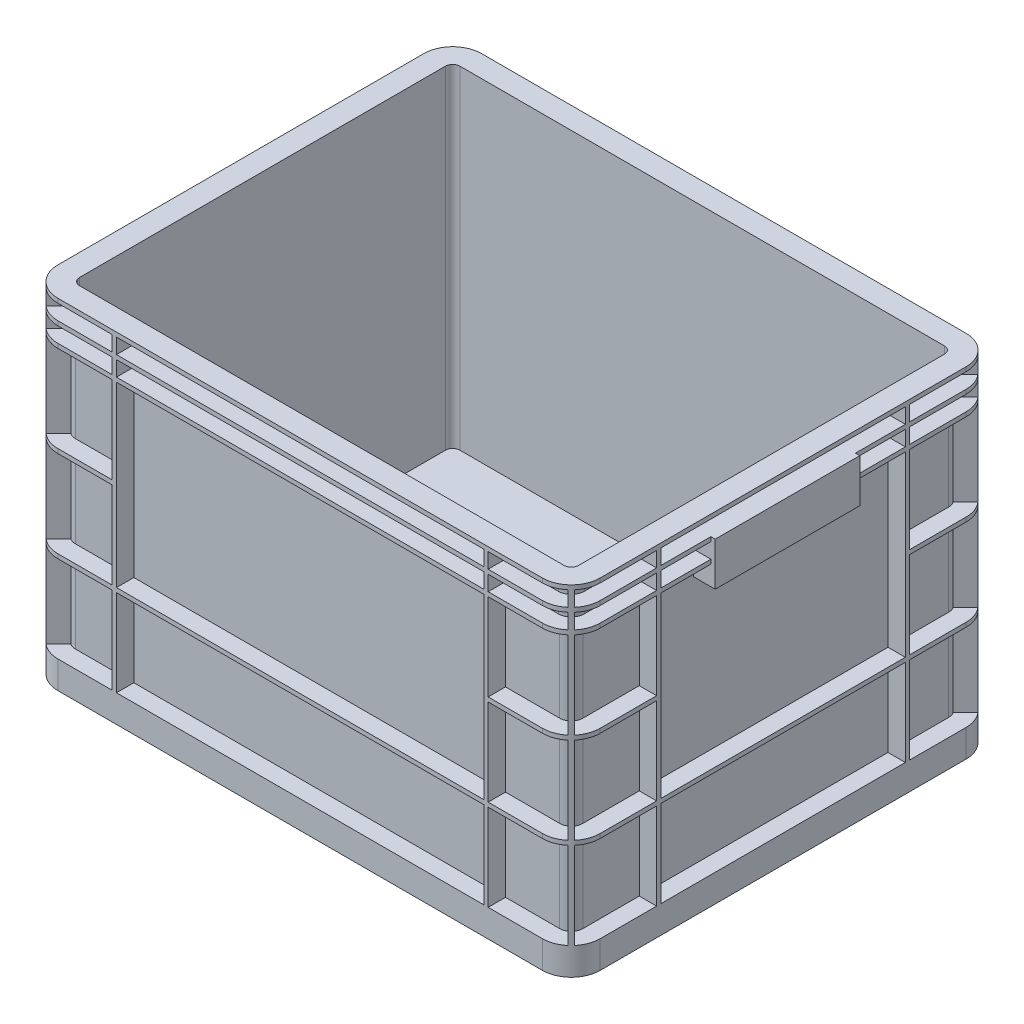
SolidWorks part; units mm, degrees
ref_plane "Front Plane" through (0, 0, 0) normal (0, 0, 1) x (1, 0, 0)
ref_plane "Top Plane" through (0, 0, 0) normal (0, 1, 0) x (1, 0, 0)
ref_plane "Right Plane" through (0, 0, 0) normal (1, 0, 0) x (0, 0, -1)
sketch "Sketch1" plane through (0, 0, 0) normal (0, 1, 0) x (1, 0, 0)
  line L1 (0, 0) -> (375, 0)
  line L2 (0, 0) -> (0, 293)
  line L3 (0, 293) -> (375, 293)
  line L4 (375, 0) -> (375, 293)
  dimension "D1" = 375
  dimension "D2" = 293
extrude "Boss-Extrude1" add sketch "Sketch1" along normal blind 240
fillet "Fillet1" radius 20 4 edges at (0, 120, -293) (375, 120, -293) (0, 120, 0) (375, 120, 0)
sketch "Sketch2" plane through (0, 240, 0) normal (0, 1, 0) x (1, 0, 0)
  line L8 (355, 278) -> (20, 278)
  line L9 (15, 273) -> (15, 20)
  line L10 (20, 15) -> (355, 15)
  line L11 (360, 20) -> (360, 273)
  line L12 (355, 278) -> (20, 278)
  line L13 (15, 273) -> (15, 20)
  line L14 (20, 15) -> (355, 15)
  line L15 (360, 20) -> (360, 273)
  arc A8 (20, 278) -> (15, 273) centre (20, 273) ccw
  arc A9 (15, 20) -> (20, 15) centre (20, 20) ccw
  arc A10 (355, 15) -> (360, 20) centre (355, 20) ccw
  arc A11 (360, 273) -> (355, 278) centre (355, 273) ccw
  arc A12 (20, 278) -> (15, 273) centre (20, 273) ccw
  arc A13 (15, 20) -> (20, 15) centre (20, 20) ccw
  arc A14 (355, 15) -> (360, 20) centre (355, 20) ccw
  arc A15 (360, 273) -> (355, 278) centre (355, 273) ccw
  dimension "D1" = 15
extrude "Cut-Extrude1" cut sketch "Sketch2" against normal blind 230
sketch "Sketch3" plane through (0, 0, 0) normal (0, -1, 0) x (1, 0, 0)
  line L0 (365, -273) -> (365, -20)
  line L1 (355, -10) -> (20, -10)
  line L2 (10, -20) -> (10, -273)
  line L3 (20, -283) -> (355, -283)
  line L4 (0, -20) -> (0, -273)
  line L5 (20, -293) -> (355, -293)
  line L6 (375, -273) -> (375, -20)
  line L7 (355, 0) -> (20, 0)
  line L8 (0, -20) -> (0, -273)
  line L9 (20, -293) -> (355, -293)
  line L10 (375, -273) -> (375, -20)
  line L11 (355, 0) -> (20, 0)
  arc A0 (365, -20) -> (355, -10) centre (355, -20) ccw
  arc A1 (20, -10) -> (10, -20) centre (20, -20) ccw
  arc A2 (10, -273) -> (20, -283) centre (20, -273) ccw
  arc A3 (355, -283) -> (365, -273) centre (355, -273) ccw
  arc A4 (0, -273) -> (20, -293) centre (20, -273) ccw
  arc A5 (355, -293) -> (375, -273) centre (355, -273) ccw
  arc A6 (375, -20) -> (355, 0) centre (355, -20) ccw
  arc A7 (20, 0) -> (0, -20) centre (20, -20) ccw
  arc A8 (0, -273) -> (20, -293) centre (20, -273) ccw
  arc A9 (355, -293) -> (375, -273) centre (355, -273) ccw
  arc A10 (375, -20) -> (355, 0) centre (355, -20) ccw
  arc A11 (20, 0) -> (0, -20) centre (20, -20) ccw
  dimension "D1" = 0
  dimension "D2" = 10
extrude "Cut-Extrude2" cut sketch "Sketch3" against normal blind 5
sketch "Sketch4" plane through (0, 0, 0) normal (0, -1, 0) x (1, 0, 0)
  line L4 (20, -283) -> (355, -283)
  line L5 (365, -273) -> (365, -20)
  line L6 (355, -10) -> (20, -10)
  line L7 (10, -20) -> (10, -273)
  line L8 (20, -283) -> (355, -283)
  line L9 (365, -273) -> (365, -20) construction
  line L10 (355, -10) -> (20, -10)
  line L11 (10, -20) -> (10, -273)
  line L16 (20, -278) -> (355, -278)
  line L17 (360, -273) -> (360, -20)
  line L18 (355, -15) -> (20, -15)
  line L19 (15, -20) -> (15, -273)
  line L20 (20, -278) -> (355, -278)
  line L21 (360, -273) -> (360, -20)
  line L22 (355, -15) -> (20, -15)
  line L23 (15, -20) -> (15, -273)
  arc A4 (355, -283) -> (365, -273) centre (355, -273) ccw
  arc A5 (365, -20) -> (355, -10) centre (355, -20) ccw
  arc A6 (20, -10) -> (10, -20) centre (20, -20) ccw
  arc A7 (10, -273) -> (20, -283) centre (20, -273) ccw
  arc A8 (355, -283) -> (365, -273) centre (355, -273) ccw
  arc A9 (365, -20) -> (355, -10) centre (355, -20) ccw construction
  arc A10 (20, -10) -> (10, -20) centre (20, -20) ccw
  arc A11 (10, -273) -> (20, -283) centre (20, -273) ccw
  arc A16 (355, -278) -> (360, -273) centre (355, -273) ccw
  arc A17 (360, -20) -> (355, -15) centre (355, -20) ccw
  arc A18 (20, -15) -> (15, -20) centre (20, -20) ccw
  arc A19 (15, -273) -> (20, -278) centre (20, -273) ccw
  arc A20 (355, -278) -> (360, -273) centre (355, -273) ccw
  arc A21 (360, -20) -> (355, -15) centre (355, -20) ccw
  arc A22 (20, -15) -> (15, -20) centre (20, -20) ccw
  arc A23 (15, -273) -> (20, -278) centre (20, -273) ccw
  dimension "D1" = 0
  dimension "D2" = 5
extrude "Cut-Extrude3" cut sketch "Sketch4" against normal blind 5 contours L23 A23 L20 A20 L21 A21 L22 A22
ref_plane "Plane2" through (0, 210, 0) normal (0, 1, 0) x (1, 0, 0)
sketch "Sketch5" plane through (0, 210, 0) normal (0, 1, 0) x (1, 0, 0)
  line L4 (355, 293) -> (20, 293)
  line L5 (0, 273) -> (0, 20)
  line L6 (20, 0) -> (355, 0)
  line L7 (375, 20) -> (375, 273)
  line L8 (355, 293) -> (20, 293)
  line L9 (0, 273) -> (0, 20)
  line L10 (20, 0) -> (355, 0)
  line L11 (375, 20) -> (375, 273)
  line L16 (355, 281) -> (20, 281)
  line L17 (12, 273) -> (12, 20)
  line L18 (20, 12) -> (355, 12)
  line L19 (363, 20) -> (363, 273)
  line L20 (355, 281) -> (20, 281)
  line L21 (12, 273) -> (12, 20)
  line L22 (20, 12) -> (355, 12)
  line L23 (363, 20) -> (363, 273)
  arc A4 (20, 293) -> (0, 273) centre (20, 273) ccw
  arc A5 (0, 20) -> (20, 0) centre (20, 20) ccw
  arc A6 (355, 0) -> (375, 20) centre (355, 20) ccw
  arc A7 (375, 273) -> (355, 293) centre (355, 273) ccw
  arc A8 (20, 293) -> (0, 273) centre (20, 273) ccw
  arc A9 (0, 20) -> (20, 0) centre (20, 20) ccw
  arc A10 (355, 0) -> (375, 20) centre (355, 20) ccw
  arc A11 (375, 273) -> (355, 293) centre (355, 273) ccw
  arc A16 (20, 281) -> (12, 273) centre (20, 273) ccw
  arc A17 (12, 20) -> (20, 12) centre (20, 20) ccw
  arc A18 (355, 12) -> (363, 20) centre (355, 20) ccw
  arc A19 (363, 273) -> (355, 281) centre (355, 273) ccw
  arc A20 (20, 281) -> (12, 273) centre (20, 273) ccw
  arc A21 (12, 20) -> (20, 12) centre (20, 20) ccw
  arc A22 (355, 12) -> (363, 20) centre (355, 20) ccw
  arc A23 (363, 273) -> (355, 281) centre (355, 273) ccw
  dimension "D1" = 0
  dimension "D2" = 12
extrude "Cut-Extrude4" cut sketch "Sketch5" against normal blind 60
ref_plane "Plane3" through (0, 147, 0) normal (0, 1, 0) x (1, 0, 0)
sketch "Sketch7" plane through (0, 147, 0) normal (0, 1, 0) x (1, 0, 0)
  line L0 (20, 12) -> (355, 12) construction
  line L1 (20, 12) -> (355, 12)
  line L2 (12, 273) -> (12, 20) construction
  line L3 (12, 273) -> (12, 20)
  line L4 (355, 293) -> (20, 293)
  line L5 (0, 273) -> (0, 20)
  line L6 (20, 0) -> (355, 0)
  line L7 (375, 20) -> (375, 273)
  line L8 (355, 293) -> (20, 293)
  line L9 (0, 273) -> (0, 20)
  line L10 (20, 0) -> (355, 0)
  line L11 (375, 20) -> (375, 273)
  line L12 (355, 281) -> (20, 281) construction
  line L13 (355, 281) -> (20, 281)
  line L14 (363, 20) -> (363, 273) construction
  line L15 (363, 20) -> (363, 273)
  arc A0 (12, 20) -> (20, 12) centre (20, 20) ccw construction
  arc A1 (12, 20) -> (20, 12) centre (20, 20) ccw
  arc A2 (20, 281) -> (12, 273) centre (20, 273) ccw construction
  arc A3 (20, 281) -> (12, 273) centre (20, 273) ccw
  arc A4 (375, 273) -> (355, 293) centre (355, 273) ccw
  arc A5 (20, 293) -> (0, 273) centre (20, 273) ccw
  arc A6 (0, 20) -> (20, 0) centre (20, 20) ccw
  arc A7 (355, 0) -> (375, 20) centre (355, 20) ccw
  arc A8 (375, 273) -> (355, 293) centre (355, 273) ccw
  arc A9 (20, 293) -> (0, 273) centre (20, 273) ccw
  arc A10 (0, 20) -> (20, 0) centre (20, 20) ccw
  arc A11 (355, 0) -> (375, 20) centre (355, 20) ccw
  arc A12 (363, 273) -> (355, 281) centre (355, 273) ccw construction
  arc A13 (363, 273) -> (355, 281) centre (355, 273) ccw
  arc A14 (355, 12) -> (363, 20) centre (355, 20) ccw construction
  arc A15 (355, 12) -> (363, 20) centre (355, 20) ccw
  dimension "D1" = 0
extrude "Cut-Extrude5" cut sketch "Sketch7" against normal blind 60
ref_plane "Plane4" through (0, 84, 0) normal (0, 1, 0) x (1, 0, 0)
sketch "Sketch8" plane through (0, 84, 0) normal (0, 1, 0) x (1, 0, 0)
  line L0 (363, 20) -> (363, 273) construction
  line L1 (20, 12) -> (355, 12) construction
  line L2 (12, 273) -> (12, 20) construction
  line L3 (355, 281) -> (20, 281) construction
  line L4 (355, 293) -> (20, 293)
  line L5 (0, 273) -> (0, 20)
  line L6 (20, 0) -> (355, 0)
  line L7 (375, 20) -> (375, 273)
  line L8 (355, 293) -> (20, 293)
  line L9 (0, 273) -> (0, 20)
  line L10 (20, 0) -> (355, 0)
  line L11 (375, 20) -> (375, 273)
  line L12 (363, 20) -> (363, 273)
  line L13 (20, 12) -> (355, 12)
  line L14 (12, 273) -> (12, 20)
  line L15 (355, 281) -> (20, 281)
  arc A0 (355, 12) -> (363, 20) centre (355, 20) ccw construction
  arc A1 (12, 20) -> (20, 12) centre (20, 20) ccw construction
  arc A2 (20, 281) -> (12, 273) centre (20, 273) ccw construction
  arc A3 (363, 273) -> (355, 281) centre (355, 273) ccw construction
  arc A4 (375, 273) -> (355, 293) centre (355, 273) ccw
  arc A5 (20, 293) -> (0, 273) centre (20, 273) ccw
  arc A6 (0, 20) -> (20, 0) centre (20, 20) ccw
  arc A7 (355, 0) -> (375, 20) centre (355, 20) ccw
  arc A8 (375, 273) -> (355, 293) centre (355, 273) ccw
  arc A9 (20, 293) -> (0, 273) centre (20, 273) ccw
  arc A10 (0, 20) -> (20, 0) centre (20, 20) ccw
  arc A11 (355, 0) -> (375, 20) centre (355, 20) ccw
  arc A12 (355, 12) -> (363, 20) centre (355, 20) ccw
  arc A13 (12, 20) -> (20, 12) centre (20, 20) ccw
  arc A14 (20, 281) -> (12, 273) centre (20, 273) ccw
  arc A15 (363, 273) -> (355, 281) centre (355, 273) ccw
  dimension "D1" = 0
extrude "Cut-Extrude6" cut sketch "Sketch8" against normal blind 60
ref_plane "Plane8" through (0, 237, 0) normal (0, 1, 0) x (1, 0, 0)
sketch "Sketch16" plane through (0, 237, 0) normal (0, 1, 0) x (1, 0, 0)
  line L0 (355, 282) -> (20, 282)
  line L1 (11, 273) -> (11, 20)
  line L2 (20, 11) -> (355, 11)
  line L3 (364, 20) -> (364, 273)
  line L4 (355, 293) -> (20, 293)
  line L5 (0, 273) -> (0, 20)
  line L6 (20, 0) -> (355, 0)
  line L7 (375, 20) -> (375, 273)
  line L8 (355, 293) -> (20, 293)
  line L9 (0, 273) -> (0, 20)
  line L10 (20, 0) -> (355, 0)
  line L11 (375, 20) -> (375, 273)
  arc A0 (20, 282) -> (11, 273) centre (20, 273) ccw
  arc A1 (11, 20) -> (20, 11) centre (20, 20) ccw
  arc A2 (355, 11) -> (364, 20) centre (355, 20) ccw
  arc A3 (364, 273) -> (355, 282) centre (355, 273) ccw
  arc A4 (20, 293) -> (0, 273) centre (20, 273) ccw
  arc A5 (0, 20) -> (20, 0) centre (20, 20) ccw
  arc A6 (355, 0) -> (375, 20) centre (355, 20) ccw
  arc A7 (375, 273) -> (355, 293) centre (355, 273) ccw
  arc A8 (20, 293) -> (0, 273) centre (20, 273) ccw
  arc A9 (0, 20) -> (20, 0) centre (20, 20) ccw
  arc A10 (355, 0) -> (375, 20) centre (355, 20) ccw
  arc A11 (375, 273) -> (355, 293) centre (355, 273) ccw
  dimension "D1" = 0
  dimension "D2" = 11
extrude "Cut-Extrude12" cut sketch "Sketch16" against normal blind 10.5
ref_plane "Plane9" through (0, 223.5, 0) normal (0, 1, 0) x (1, 0, 0)
sketch "Sketch17" plane through (0, 223.5, 0) normal (0, 1, 0) x (1, 0, 0)
  line L0 (355, 282) -> (20, 282)
  line L1 (11, 273) -> (11, 20)
  line L2 (20, 11) -> (355, 11)
  line L3 (364, 20) -> (364, 273)
  line L4 (355, 293) -> (20, 293)
  line L5 (0, 273) -> (0, 20)
  line L6 (20, 0) -> (355, 0)
  line L7 (375, 20) -> (375, 273)
  line L8 (355, 293) -> (20, 293)
  line L9 (0, 273) -> (0, 20)
  line L10 (20, 0) -> (355, 0)
  line L11 (375, 20) -> (375, 273)
  arc A0 (20, 282) -> (11, 273) centre (20, 273) ccw
  arc A1 (11, 20) -> (20, 11) centre (20, 20) ccw
  arc A2 (355, 11) -> (364, 20) centre (355, 20) ccw
  arc A3 (364, 273) -> (355, 282) centre (355, 273) ccw
  arc A4 (20, 293) -> (0, 273) centre (20, 273) ccw
  arc A5 (0, 20) -> (20, 0) centre (20, 20) ccw
  arc A6 (355, 0) -> (375, 20) centre (355, 20) ccw
  arc A7 (375, 273) -> (355, 293) centre (355, 273) ccw
  arc A8 (20, 293) -> (0, 273) centre (20, 273) ccw
  arc A9 (0, 20) -> (20, 0) centre (20, 20) ccw
  arc A10 (355, 0) -> (375, 20) centre (355, 20) ccw
  arc A11 (375, 273) -> (355, 293) centre (355, 273) ccw
  dimension "D1" = 0
  dimension "D2" = 11
extrude "Cut-Extrude13" cut sketch "Sketch17" against normal blind 10.5
sketch "Sketch10" plane through (0, 240, 0) normal (0, 1, 0) x (1, 0, 0)
  line L0 (355, 278) -> (20, 278) construction
  line L1 (355, 278) -> (20, 278)
  line L2 (15, 273) -> (15, 20) construction
  line L3 (15, 273) -> (15, 20)
  line L4 (355, 293) -> (20, 293)
  line L5 (0, 273) -> (0, 20)
  line L6 (20, 0) -> (355, 0)
  line L7 (375, 20) -> (375, 273)
  line L8 (355, 293) -> (20, 293)
  line L9 (0, 273) -> (0, 20)
  line L10 (20, 0) -> (355, 0)
  line L11 (375, 20) -> (375, 273)
  line L12 (20, 15) -> (355, 15) construction
  line L13 (20, 15) -> (355, 15)
  line L14 (360, 20) -> (360, 273) construction
  line L15 (360, 20) -> (360, 273)
  line L16 (15.5667, 275.312) -> (4.837, 286.0416)
  line L17 (17.688, 277.4333) -> (6.9584, 288.163)
  line L19 (60.5, 278) -> (57.5, 278)
  line L20 (60.5, 278) -> (60.5, 293)
  line L21 (60.5, 293) -> (57.5, 293)
  line L22 (57.5, 278) -> (57.5, 293)
  line L23 (15, 234) -> (0, 234)
  line L24 (15, 234) -> (15, 231)
  line L25 (15, 231) -> (0, 231)
  line L26 (0, 234) -> (0, 231)
  arc A0 (20, 278) -> (15, 273) centre (20, 273) ccw construction
  arc A1 (20, 278) -> (15, 273) centre (20, 273) ccw
  arc A2 (15, 20) -> (20, 15) centre (20, 20) ccw construction
  arc A3 (15, 20) -> (20, 15) centre (20, 20) ccw
  arc A4 (20, 293) -> (0, 273) centre (20, 273) ccw
  arc A5 (0, 20) -> (20, 0) centre (20, 20) ccw
  arc A6 (355, 0) -> (375, 20) centre (355, 20) ccw
  arc A7 (375, 273) -> (355, 293) centre (355, 273) ccw
  arc A8 (20, 293) -> (0, 273) centre (20, 273) ccw
  arc A9 (0, 20) -> (20, 0) centre (20, 20) ccw
  arc A10 (355, 0) -> (375, 20) centre (355, 20) ccw
  arc A11 (375, 273) -> (355, 293) centre (355, 273) ccw
  arc A12 (355, 15) -> (360, 20) centre (355, 20) ccw construction
  arc A13 (355, 15) -> (360, 20) centre (355, 20) ccw
  arc A14 (360, 273) -> (355, 278) centre (355, 273) ccw construction
  arc A15 (360, 273) -> (355, 278) centre (355, 273) ccw
  point P24 (16.4645, 276.5355)
  point P29 (187.5, 293)
  point P34 (0, 146.5)
  arc M23 (15, 273) -> (20, 278) centre (20, 273) cw
  arc M25 (20, 293) -> (0, 273) centre (20, 273) ccw
  dimension "D2" = 3
  dimension "D3" = 45
  dimension "D4" = 1.5
  dimension "D5" = 3
  dimension "D6" = 130
  dimension "D7" = 3
  dimension "D8" = 87.5
  dimension "D1" = 0
extrude "Boss-Extrude2" add sketch "Sketch10" against normal up to surface (216 mm away) contours L25 L3 L23 L9 | L17 L16 M23 M25 | L22 L1 L20 L8 up to face at (187.5, 24, -146.5)
ref_plane "Plane5" through (0, 0, -146.5) normal (0, 0, 1) x (1, 0, 0)
mirror "Mirror1" about plane through (0, 0, -146.5) normal (0, 0, 1) of "Boss-Extrude2"
ref_plane "Plane6" through (187.5, 0, 0) normal (1, 0, 0) x (0, 0, -1)
mirror "Mirror2" about plane through (187.5, 0, 0) normal (1, 0, 0) of "Mirror1", "Boss-Extrude2"
sketch "Sketch11" plane through (0, 150, 0) normal (0, 1, 0) x (1, 0, 0)
  line L4 (314.5, 0) -> (314.5, 12)
  line L5 (314.5, 12) -> (60.5, 12)
  line L6 (60.5, 12) -> (60.5, 0)
  line L7 (60.5, 0) -> (314.5, 0)
  line L8 (314.5, 0) -> (314.5, 12)
  line L9 (314.5, 12) -> (60.5, 12)
  line L10 (60.5, 12) -> (60.5, 0)
  line L11 (60.5, 0) -> (314.5, 0)
  dimension "D1" = 0
extrude "Cut-Extrude7" cut sketch "Sketch11" against normal blind 42
sketch "Sketch12" plane through (0, 150, 0) normal (0, 1, 0) x (1, 0, 0)
  line L4 (0, 62) -> (12, 62)
  line L5 (12, 62) -> (12, 231)
  line L6 (12, 231) -> (0, 231)
  line L7 (0, 231) -> (0, 62)
  line L8 (0, 62) -> (12, 62)
  line L9 (12, 62) -> (12, 231)
  line L10 (12, 231) -> (0, 231)
  line L11 (0, 231) -> (0, 62)
  dimension "D1" = 0
extrude "Cut-Extrude8" cut sketch "Sketch12" against normal blind 42
sketch "Sketch13" plane through (0, 150, 0) normal (0, 1, 0) x (1, 0, 0)
  line L4 (60.5, 281) -> (314.5, 281)
  line L5 (314.5, 281) -> (314.5, 293)
  line L6 (314.5, 293) -> (60.5, 293)
  line L7 (60.5, 293) -> (60.5, 281)
  line L8 (60.5, 281) -> (314.5, 281)
  line L9 (314.5, 281) -> (314.5, 293)
  line L10 (314.5, 293) -> (60.5, 293)
  line L11 (60.5, 293) -> (60.5, 281)
  dimension "D1" = 0
extrude "Cut-Extrude9" cut sketch "Sketch13" against normal blind 42
sketch "Sketch14" plane through (0, 150, 0) normal (0, 1, 0) x (1, 0, 0)
  line L4 (375, 231) -> (363, 231)
  line L5 (363, 231) -> (363, 62)
  line L6 (363, 62) -> (375, 62)
  line L7 (375, 62) -> (375, 231)
  line L8 (375, 231) -> (363, 231)
  line L9 (363, 231) -> (363, 62)
  line L10 (363, 62) -> (375, 62)
  line L11 (375, 62) -> (375, 231)
  dimension "D1" = 0
extrude "Cut-Extrude10" cut sketch "Sketch14" against normal blind 42
sketch "Sketch19" plane through (0, 0, 0) normal (-1, 0, 0) x (0, 0, 1)
  line L0 (-231, 226.5) -> (-62, 226.5) construction
  line L1 (-196.5, 226.5) -> (-96.5, 226.5)
  line L2 (-196.5, 226.5) -> (-196.5, 196.5)
  line L3 (-196.5, 196.5) -> (-96.5, 196.5)
  line L4 (-96.5, 226.5) -> (-96.5, 196.5)
  line L5 (-273, 240) -> (-20, 240) construction
  line L6 (-20, 0) -> (-273, 0) construction
  point P6 (-146.5, 240)
  point P9 (-146.5, 196.5)
  dimension "D1" = 100
  dimension "D2" = 30
  dimension "D3" = 196.5
extrude "Boss-Extrude3" add sketch "Sketch19" against normal blind 15
sketch "Sketch20" plane through (0, 0, 0) normal (-1, 0, 0) x (0, 0, 1)
  line L0 (-231, 226.5) -> (-62, 226.5) construction
  line L1 (-196.5, 196.5) -> (-96.5, 196.5)
  line L2 (-196.5, 196.5) -> (-196.5, 226.5)
  line L3 (-196.5, 226.5) -> (-96.5, 226.5)
  line L4 (-96.5, 196.5) -> (-96.5, 226.5)
  line L5 (-96.5, 196.5) -> (-96.5, 210) construction
extrude "Boss-Extrude4" add sketch "Sketch20" along normal blind 3
sketch "Sketch21" plane through (0, 196.5, 0) normal (0, -1, 0) x (1, 0, 0)
  line L0 (12, -96.5) -> (12, -196.5) construction
  line L1 (12, -193.5) -> (0, -193.5)
  line L2 (12, -193.5) -> (12, -99.5)
  line L3 (12, -99.5) -> (0, -99.5)
  line L4 (0, -193.5) -> (0, -99.5)
  line L5 (-3, -196.5) -> (-3, -96.5) construction
  line L6 (12, -196.5) -> (-3, -196.5) construction
  line L7 (12, -96.5) -> (-3, -96.5) construction
  dimension "D1" = 3
  dimension "D2" = 3
  dimension "D3" = 3
extrude "Cut-Extrude14" cut sketch "Sketch21" against normal blind 25
mirror "Mirror3" about plane through (187.5, 0, 0) normal (1, 0, 0) of "Boss-Extrude3", "Boss-Extrude4", "Cut-Extrude14"
